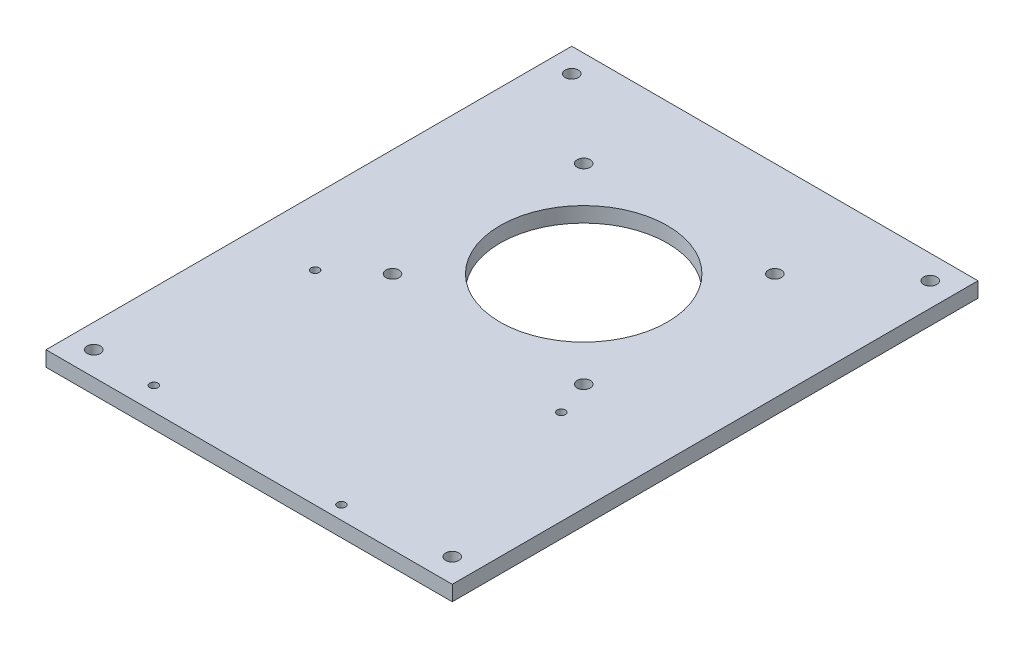
SolidWorks part; units mm, degrees
ref_plane "Front Plane" through (0, 0, 0) normal (0, 0, 1) x (1, 0, 0)
ref_plane "Top Plane" through (0, 0, 0) normal (0, 1, 0) x (1, 0, 0)
ref_plane "Right Plane" through (0, 0, 0) normal (1, 0, 0) x (0, 0, -1)
sketch "Sketch2" plane through (0, 0, 0) normal (0, 1, 0) x (1, 0, 0)
  line L0 (0, 61.8644) -> (0, -41.9492) construction
  line L1 (45.7627, 0) -> (-92.7966, 0) construction
  line L3 (-85, 80) -> (85, 80)
  line L4 (-85, 80) -> (-85, -140)
  line L5 (-85, -140) -> (85, -140)
  line L6 (85, 80) -> (85, -140)
  circle A0 centre (0, 0) radius 35
  circle A1 centre (-40, 40) radius 2.75
  circle A2 centre (40, 40) radius 2.75
  circle A3 centre (40, -40) radius 2.75
  circle A4 centre (-40, -40) radius 2.75
  circle A5 centre (-75, 70) radius 2.75
  circle A6 centre (-75, -130) radius 2.75
  circle A7 centre (75, 70) radius 2.75
  circle A8 centre (75, -130) radius 2.75
  dimension "D3" = 80
  dimension "D4" = 70
  dimension "D5" = 5.5
  dimension "D6" = 40
  dimension "D8" = 5.5
  dimension "D14" = 5.5
  dimension "D1" = 170
  dimension "D2" = 220
  dimension "D7" = 40
  dimension "D9" = 10
  dimension "D10" = 10
  dimension "D11" = 10
  dimension "D12" = 10
  dimension "D13" = 85
extrude "Boss-Extrude1" add sketch "Sketch2" along normal blind 6.35
sketch "Sketch4" plane through (5.335, 6.35, 187.9656) normal (0, 1, 0) x (-1, 0, 0)
  point P1 (62.8581, -133.1056)
  point P6 (54.8581, -57.6056)
  point P10 (-27.6419, -53.6056)
  point P14 (-40.1419, -133.1056)
hole_wizard "CSK for M3 Flat Head Machine Screw2" positions "Sketch8" profile "Sketch7" countersink size "M3" standard "ANSI Metric" end condition through all
sketch "Sketch8" plane through (0, 0, 0) normal (0, -1, 0) x (-1, 0, 0)
  point P0 (57.5231, -54.86)
  point P2 (-45.4769, -54.86)
  point P4 (-32.9769, -134.36)
  point P6 (49.5231, -130.36)
sketch "Sketch7" plane through (-57.5231, 0, 54.86) normal (1, 0, 0) x (0, 0, -1)
  line L0 (0, 0) -> (0, 6.35)
  line L1 (0, 6.35) -> (1.7, 6.35)
  line L2 (1.7, 6.35) -> (1.7, 1.45)
  line L3 (1.7, 1.45) -> (3.15, 0)
  line L5 (3.15, 0) -> (0, 0)
  line L6 (-1.7, 1.45) -> (-3.15, 0) construction
  line L11 (0, -6.35) -> (0, 107.95) construction
  dimension "Thru Hole Dia." = 3.4
  dimension "Thru Hole Depth" = 6.35
  dimension "Near C'Sink Dia." = 6.3
  dimension "Near C'Sink Angle" = 90
equation "\"connector_D1\" = 70 'the big holes diameter"
equation "\"mtg_hole_D\" = 5.5 'mounting holes"
equation "\"mtg_dfc\" = 40 'mounting hole distance from center"
equation "\"plate_thickness\" = 6.35 'thickness of the plate "
equation "\"t_height\" = 200"
equation "\"t_width\" = 240"
equation "\"t_length\" = 240"
equation "\"plate_hole_from_edge\" = 9"
equation "\"plate_spacing\" = 1"
equation "\"front_plate_height\" = \"t_height\" + 38"
equation "\"front_plate_width\" = \"t_width\" + 38"
equation "\"side_plate_height\" = \"front_plate_height\""
equation "\"side_plate_length\" = \"t_length\" + 38"
equation "\"top_plate_width\" = \"front_plate_width\""
equation "\"top_plate_length\" = \"side_plate_length\""
equation "\"itx_support_t_slot_length\" = \"t_width\" + (2 * 20.5)"
equation "\"locomotion_length\" = \"t_length\""
equation "\"locomotion_width\" = \"t_width\""
equation "\"locomotion_height\" = 40"
equation "\"itx_mtg_hole_spacing\" = 40"
equation "\"emg30_bracket_hole_len\" = 60"
equation "\"emg30_bracket_hole_wid\" = 11"
equation "\"perce_t_height\" = 50"
equation "\"perce_top_width\" = 170"
equation "\"perce_mtg_hole_spacing\" = \"perce_top_width\" - 20"
equation "\"D1@Sketch2\"=\"perce_top_width\""
equation "\"D1@Boss-Extrude1\"=\"plate_thickness\""
equation "\"D5@Sketch2\"=\"mtg_hole_D\""
equation "\"D4@Sketch2\"=\"connector_D1\""
equation "\"D6@Sketch2\"=\"mtg_dfc\""
equation "\"D7@Sketch2\"=\"mtg_dfc\""
equation "\"D8@Sketch2\"=\"mtg_hole_D\""
equation "\"D13@Sketch2\"=\"D1@Sketch2\"/2"
equation "\"D14@Sketch2\"=\"mtg_hole_D\""
